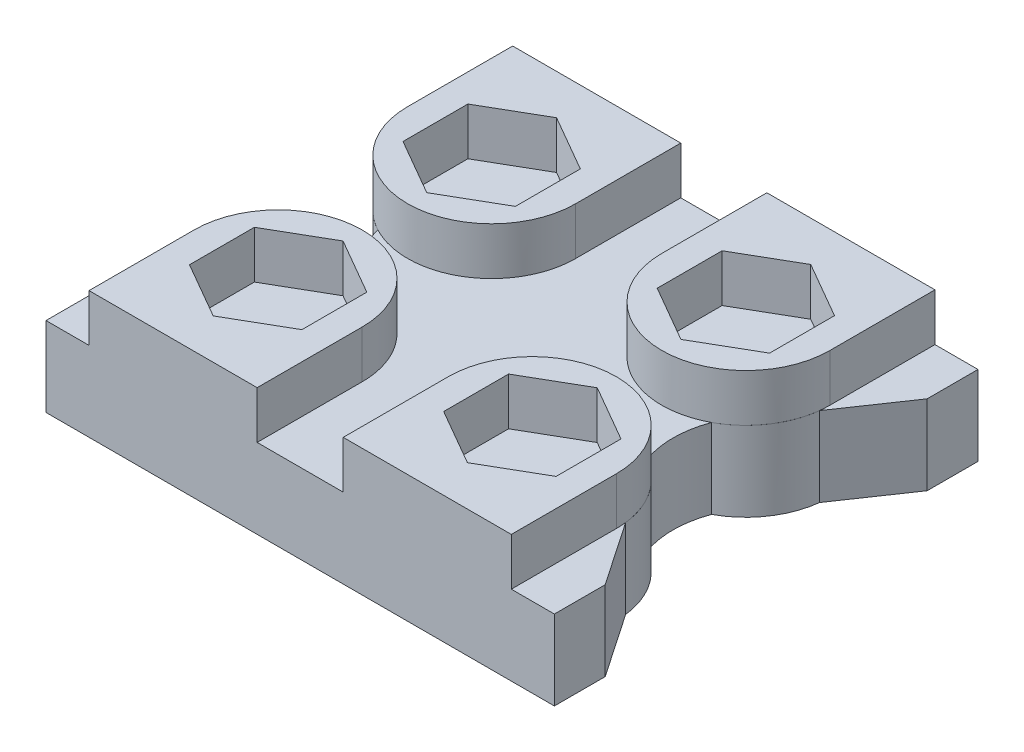
SolidWorks part; units mm, degrees
material "Rubber"
ref_plane "Front Plane" through (0, 0, 0) normal (0, 0, 1) x (1, 0, 0)
ref_plane "Top Plane" through (0, 0, 0) normal (0, 1, 0) x (1, 0, 0)
ref_plane "Right Plane" through (0, 0, 0) normal (1, 0, 0) x (0, 0, -1)
sketch "Sketch1" plane through (0, 0, 0) normal (0, 1, 0) x (1, 0, 0)
  line L0 (0, 0) -> (0, 3) construction
  line L1 (0, 0) -> (30, 0)
  line L2 (15, 25) -> (15, 0) construction
  line L3 (0, 25) -> (30, 25)
  line L5 (7.5, 0) -> (7.5, 6.2) construction
  line L6 (7.5, 18.8) -> (7.5, 25) construction
  line L7 (7.5, 18.8) -> (7.5, 6.2) construction
  line L8 (0, 12.5) -> (7.5, 12.5) construction
  line L9 (7.5, 6.2) -> (22.5, 6.2) construction
  line L10 (7.5, 18.8) -> (22.5, 18.8) construction
  line L11 (22.5, 18.8) -> (22.5, 6.2) construction
  line L12 (22.5, 12.5) -> (30, 12.5) construction
  line L13 (0, 25) -> (0, 22)
  line L14 (30, 0) -> (30, 3)
  line L15 (0, 0) -> (0, 3)
  line L16 (0, 3) -> (2.5716, 6.7764)
  line L17 (0, 22) -> (2.5716, 18.2236)
  line L18 (30, 3) -> (27.4284, 6.7764)
  line L19 (30, 22) -> (27.4284, 18.2236)
  line L20 (30, 25) -> (30, 22)
  arc A0 (2.5716, 6.7764) -> (5.1496, 10.5701) centre (7.5, 6.2) cw
  arc A1 (2.5716, 18.2236) -> (5.1496, 14.4299) centre (7.5, 18.8) ccw
  arc A2 (27.4284, 6.7764) -> (24.8504, 10.5701) centre (22.5, 6.2) ccw
  arc A3 (24.8504, 10.5701) -> (24.8504, 14.4299) centre (30, 12.5) cw
  arc A4 (5.1496, 10.5701) -> (5.1496, 14.4299) centre (0, 12.5) ccw
  arc A5 (27.4284, 18.2236) -> (24.8504, 14.4299) centre (22.5, 18.8) cw
  point P5 (0, 12.5)
  point P6 (30, 12.5)
extrude "Extrude2" add sketch "Sketch1" along normal blind 4.7
sketch "Sketch3" plane through (0, 4.7, 0) normal (0, 1, 0) x (1, 0, 0)
  line L0 (7.5, 6.2) -> (22.5, 6.2) construction
  line L1 (7.5, 18.8) -> (22.5, 18.8) construction
  line L2 (2.54, 6.2) -> (2.54, 0)
  line L3 (0, 0) -> (30, 0) construction
  line L4 (12.46, 6.2) -> (12.46, 0)
  line L5 (2.54, 18.8) -> (2.54, 25)
  line L6 (0, 25) -> (30, 25) construction
  line L7 (12.46, 18.8) -> (12.46, 25)
  line L8 (2.54, 0) -> (12.46, 0)
  line L9 (2.54, 25) -> (12.46, 25)
  line L10 (15, 25) -> (15, 0) construction
  line L11 (15, 25) -> (15, 0) construction
  line L12 (27.46, 0) -> (17.54, 0)
  line L13 (7.5, 18.8) -> (7.5, 25) construction
  line L14 (27.46, 6.2) -> (27.46, 0)
  line L15 (7.5, 18.8) -> (7.5, 6.2) construction
  line L16 (17.54, 6.2) -> (17.54, 0)
  line L17 (19.1831, 4.285) -> (19.1831, 8.115)
  line L18 (7.5, 0) -> (7.5, 6.2) construction
  line L19 (22.5, 2.37) -> (19.1831, 4.285)
  line L20 (25.8169, 4.285) -> (22.5, 2.37)
  line L21 (25.8169, 8.115) -> (25.8169, 4.285)
  line L22 (22.5, 10.03) -> (25.8169, 8.115)
  line L23 (19.1831, 8.115) -> (22.5, 10.03)
  line L24 (7.5, 22.63) -> (4.1831, 20.715)
  line L25 (4.1831, 20.715) -> (4.1831, 16.885)
  line L26 (4.1831, 16.885) -> (7.5, 14.97)
  line L27 (7.5, 14.97) -> (10.8169, 16.885)
  line L28 (10.8169, 16.885) -> (10.8169, 20.715)
  line L29 (10.8169, 20.715) -> (7.5, 22.63)
  line L30 (7.5, 10.03) -> (4.1831, 8.115)
  line L31 (4.1831, 8.115) -> (4.1831, 4.285)
  line L32 (4.1831, 4.285) -> (7.5, 2.37)
  line L33 (7.5, 2.37) -> (10.8169, 4.285)
  line L34 (10.8169, 4.285) -> (10.8169, 8.115)
  line L35 (10.8169, 8.115) -> (7.5, 10.03)
  line L36 (25.8169, 16.885) -> (22.5, 14.97)
  line L37 (22.5, 14.97) -> (19.1831, 16.885)
  line L38 (19.1831, 16.885) -> (19.1831, 20.715)
  line L39 (19.1831, 20.715) -> (22.5, 22.63)
  line L40 (22.5, 22.63) -> (25.8169, 20.715)
  line L41 (25.8169, 20.715) -> (25.8169, 16.885)
  line L42 (17.54, 18.8) -> (17.54, 25)
  line L43 (27.46, 25) -> (17.54, 25)
  line L44 (27.46, 18.8) -> (27.46, 25)
  arc A0 (12.46, 6.2) -> (2.54, 6.2) centre (7.5, 6.2) ccw
  arc A1 (12.46, 18.8) -> (2.54, 18.8) centre (7.5, 18.8) cw
  arc A2 (17.54, 6.2) -> (27.46, 6.2) centre (22.5, 6.2) cw
  arc A3 (17.54, 18.8) -> (27.46, 18.8) centre (22.5, 18.8) ccw
  circle A4 centre (7.5, 18.8) radius 3.3169 construction
  circle A5 centre (7.5, 6.2) radius 3.3169 construction
extrude "Extrude3" add sketch "Sketch3" along normal blind 2.8
